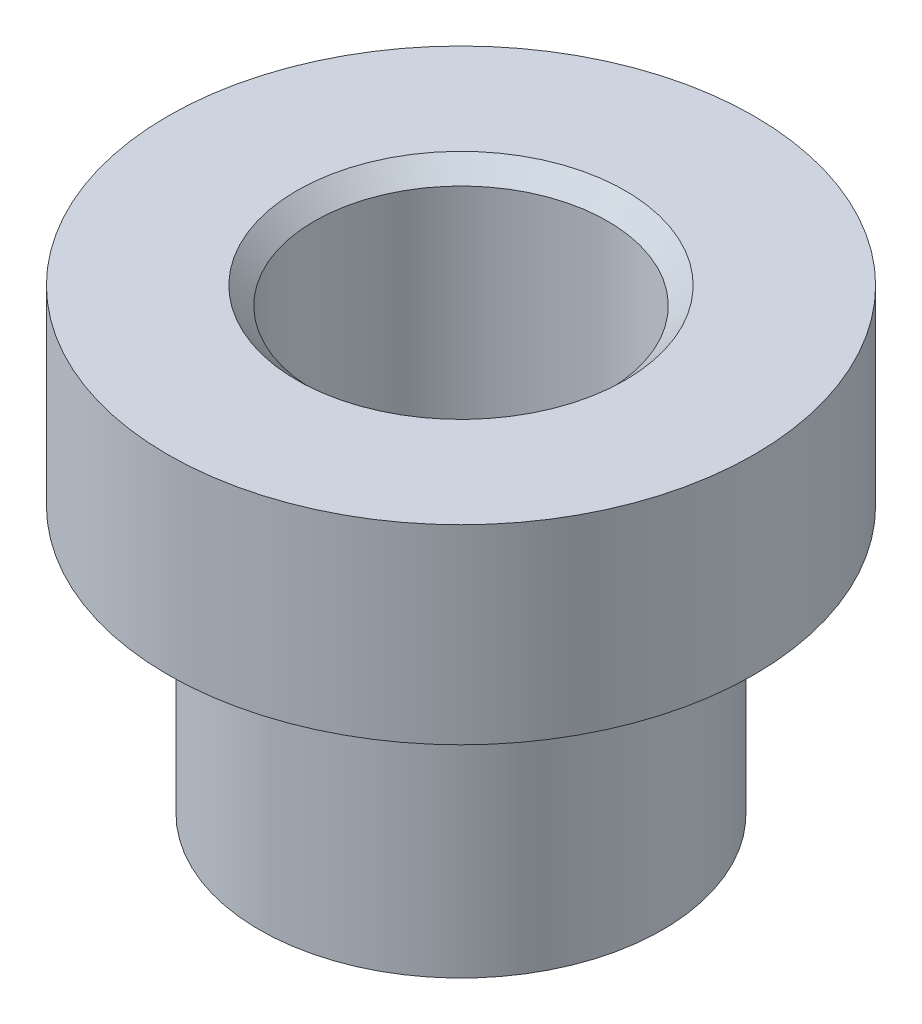
SolidWorks part; units mm, degrees
material "Delrin 2700 NC010, Low Viscosity Acetal Copolymer (SS)"
ref_plane "Front Plane" through (0, 0, 0) normal (0, 0, 1) x (1, 0, 0)
ref_plane "Top Plane" through (0, 0, 0) normal (0, 1, 0) x (1, 0, 0)
ref_plane "Right Plane" through (0, 0, 0) normal (1, 0, 0) x (0, 0, -1)
sketch "Sketch1" plane through (0, 0, 0) normal (0, 0, 1) x (1, 0, 0)
  line L0 (8.7313, 0) -> (12.7, 0)
  line L1 (12.7, 0) -> (12.7, 8.255)
  line L2 (12.7, 8.255) -> (6.35, 8.255)
  line L3 (6.35, 8.255) -> (6.35, -11.049)
  line L4 (6.35, -11.049) -> (0, -11.049)
  line L5 (0, -11.049) -> (0, -11.557)
  line L6 (0, -11.557) -> (8.7313, -11.557)
  line L7 (8.7313, -11.557) -> (8.7313, 0)
  dimension "D1" = 6.35
  dimension "D2" = 2.3813
  dimension "D3" = 12.7
  dimension "D4" = 8.255
  dimension "D5" = 19.304
  dimension "D6" = 0.508
revolve "Revolve1" add sketch "Sketch1" angle 360 about L5
chamfer "Chamfer1" distance 0.762 angle 45 1 edges at (-6.35, 8.255, 0)
